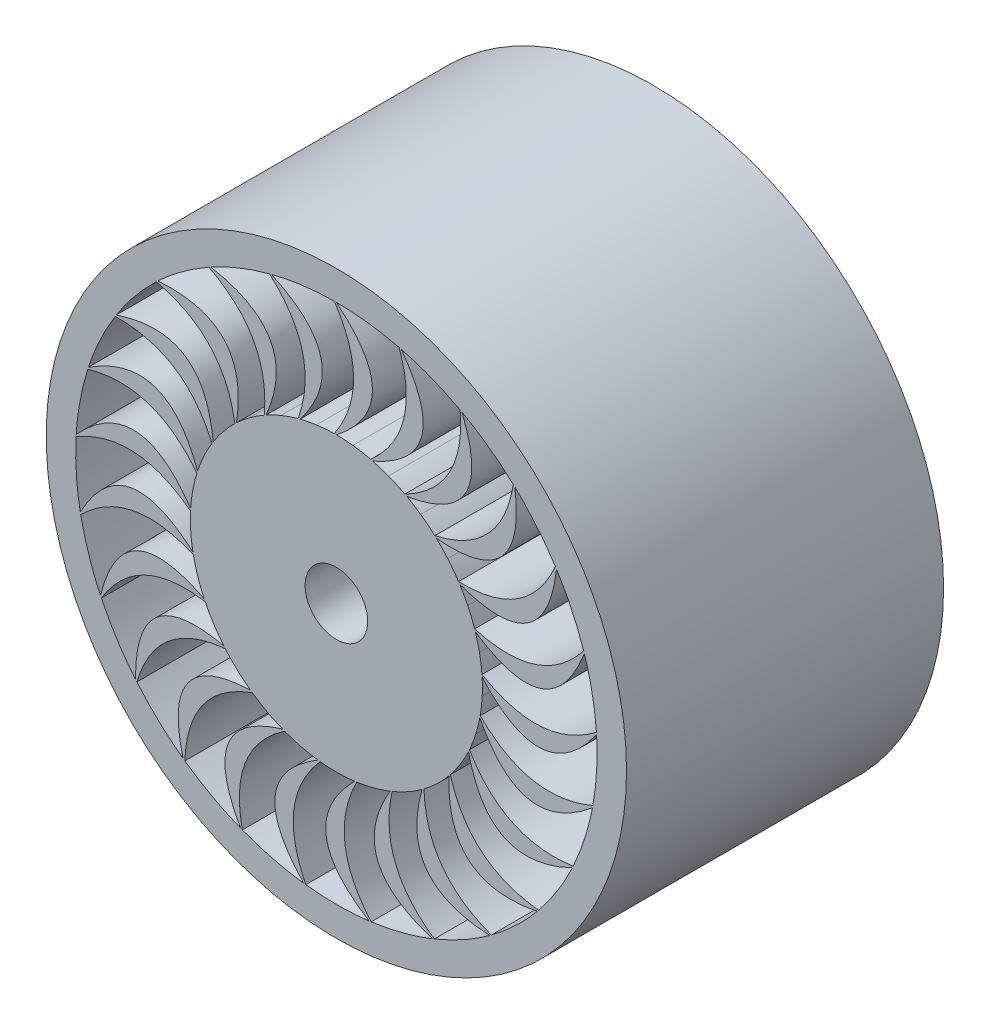
SolidWorks part; units mm, degrees
ref_plane "Front Plane" through (0, 0, 0) normal (0, 0, 1) x (1, 0, 0)
ref_plane "Top Plane" through (0, 0, 0) normal (0, 1, 0) x (1, 0, 0)
ref_plane "Right Plane" through (0, 0, 0) normal (1, 0, 0) x (0, 0, -1)
sketch "Sketch1" plane through (0, 0, 0) normal (0, 0, 1) x (1, 0, 0)
  circle A0 centre (0, 0) radius 50
  circle A1 centre (0, 0) radius 70
extrude "Boss-Extrude1" add sketch "Sketch1" along normal blind 30
sketch "Sketch2" plane through (0, 0, 30) normal (0, 0, 1) x (1, 0, 0)
  circle A0 centre (0, 0) radius 70
  circle A1 centre (0, 0) radius 34
extrude "Boss-Extrude2" add sketch "Sketch2" along normal blind 92
sketch "Sketch3" plane through (0, 0, 122) normal (0, 0, 1) x (1, 0, 0)
  circle A0 centre (0, 0) radius 15
  circle A1 centre (0, 0) radius 70
extrude "Boss-Extrude3" add sketch "Sketch3" along normal blind 30
sketch "Sketch5" plane through (0, 0, 152) normal (0, 0, 1) x (1, 0, 0)
  circle A0 centre (0, 0) radius 63.2151
  circle A1 centre (0, 0) radius 139.1054
  spline S0 degree 2 poles (0, 125) (34.5207, 97.0004) (0, 70) knots 0 0 0 1 1 1
  spline S1 degree 2 poles (-1, 124.996) (17.4362, 97.3198) (-1, 70) knots 0 0 0 1 1 1
  spline S2 degree 2 poles (30.1167, 121.3177) (41.0908, 89.9262) (16.4397, 68.0495) knots 0 0 0 1 1 1
  spline S3 degree 2 poles (31.0862, 121.0729) (57.5592, 85.368) (17.4083, 67.8008) knots 0 0 0 1 1 1
  spline S4 degree 2 poles (59.341, 110.0166) (62.1636, 76.8821) (32.8465, 61.8232) knots 0 0 0 1 1 1
  spline S5 degree 2 poles (60.2192, 109.5383) (76.981, 68.3717) (33.7228, 61.3415) knots 0 0 0 1 1 1
  spline S6 degree 2 poles (84.8367, 91.8027) (79.3304, 59.0072) (47.1893, 51.7124) knots 0 0 0 1 1 1
  spline S7 degree 2 poles (85.5684, 91.1211) (91.5659, 47.0793) (47.9183, 51.0278) knots 0 0 0 1 1 1
  spline S8 degree 2 poles (105.0018, 67.8205) (91.5126, 37.4247) (58.5671, 38.3522) knots 0 0 0 1 1 1
  spline S9 degree 2 poles (105.541, 66.9783) (100.3973, 22.8287) (59.103, 37.5079) knots 0 0 0 1 1 1
  spline S10 degree 2 poles (118.5692, 39.5769) (97.9447, 13.4907) (66.2649, 22.5822) knots 0 0 0 1 1 1
  spline S11 degree 2 poles (118.8821, 38.6271) (102.9204, -2.8563) (66.574, 21.6312) knots 0 0 0 1 1 1
  spline S12 degree 2 poles (124.6866, 8.8466) (98.2226, -11.291) (69.7991, 5.3934) knots 0 0 0 1 1 1
  spline S13 degree 2 poles (124.7533, 7.8488) (98.9766, -28.3618) (69.8619, 4.3953) knots 0 0 0 1 1 1
  spline S14 degree 2 poles (122.9694, -22.4396) (92.3288, -35.3632) (68.9475, -12.1344) knots 0 0 0 1 1 1
  spline S15 degree 2 poles (122.7859, -23.4227) (88.8138, -52.0853) (68.7601, -13.1167) knots 0 0 0 1 1 1
  spline S16 degree 2 poles (113.5255, -52.3159) (80.6337, -57.2135) (63.7637, -28.8997) knots 0 0 0 1 1 1
  spline S17 degree 2 poles (113.1034, -53.2224) (73.0704, -72.536) (63.3379, -29.8046) knots 0 0 0 1 1 1
  spline S18 degree 2 poles (96.9485, -78.9049) (63.872, -75.4688) (54.5734, -43.8492) knots 0 0 0 1 1 1
  spline S19 degree 2 poles (96.3142, -79.678) (52.7358, -88.429) (53.9359, -44.6197) knots 0 0 0 1 1 1
  spline S20 degree 2 poles (74.2798, -100.5361) (43.097, -88.9821) (41.954, -56.0434) knots 0 0 0 1 1 1
  spline S21 degree 2 poles (73.4732, -101.1271) (29.0876, -98.7657) (41.145, -56.6312) knots 0 0 0 1 1 1
  spline S22 degree 2 poles (46.9439, -115.8502) (19.6141, -96.9044) (26.6985, -64.7162) knots 0 0 0 1 1 1
  spline S23 degree 2 poles (46.0156, -116.2221) (3.6117, -102.8966) (25.7687, -65.0844) knots 0 0 0 1 1 1
  spline S24 degree 2 poles (16.6583, -123.885) (-5.1013, -98.7378) (9.7654, -69.3227) knots 0 0 0 1 1 1
  spline S25 degree 2 poles (15.6667, -124.0143) (-22.0911, -100.5621) (8.7733, -69.448) knots 0 0 0 1 1 1
  spline S26 degree 2 poles (-14.674, -124.1357) (-29.4961, -94.3671) (-7.7812, -69.5734) knots 0 0 0 1 1 1
  spline S27 degree 2 poles (-15.6667, -124.0143) (-46.4058, -91.909) (-8.7733, -69.448) knots 0 0 0 1 1 1
  spline S28 degree 2 poles (-45.0843, -116.5865) (-52.0376, -84.067) (-24.8389, -65.4525) knots 0 0 0 1 1 1
  spline S29 degree 2 poles (-46.0156, -116.2221) (-67.8047, -77.4808) (-25.7687, -65.0844) knots 0 0 0 1 1 1
  spline S30 degree 2 poles (-72.6618, -101.7117) (-71.3093, -68.4847) (-40.336, -57.219) knots 0 0 0 1 1 1
  spline S31 degree 2 poles (-73.4732, -101.1271) (-84.9432, -58.1843) (-41.145, -56.6312) knots 0 0 0 1 1 1
  spline S32 degree 2 poles (-95.6737, -80.446) (-86.1005, -48.5992) (-53.2985, -45.3902) knots 0 0 0 1 1 1
  spline S33 degree 2 poles (-96.3142, -79.678) (-96.7444, -35.2318) (-53.9359, -44.6197) knots 0 0 0 1 1 1
  spline S34 degree 2 poles (-112.674, -54.1255) (-95.4816, -25.6601) (-62.9121, -30.7094) knots 0 0 0 1 1 1
  spline S35 degree 2 poles (-113.1034, -53.2224) (-102.4668, -10.0655) (-63.3379, -29.8046) knots 0 0 0 1 1 1
  spline S36 degree 2 poles (-122.5946, -24.4042) (-98.8633, -1.1086) (-68.5727, -14.099) knots 0 0 0 1 1 1
  spline S37 degree 2 poles (-122.7859, -23.4227) (-101.7508, 15.7331) (-68.7601, -13.1167) knots 0 0 0 1 1 1
  spline S38 degree 2 poles (-124.8121, 6.8505) (-96.033, 23.5125) (-69.9247, 3.3973) knots 0 0 0 1 1 1
  spline S39 degree 2 poles (-124.7533, 7.8488) (-94.6415, 40.5433) (-69.8619, 4.3953) knots 0 0 0 1 1 1
  spline S40 degree 2 poles (-119.1873, 37.6748) (-87.1686, 46.6563) (-66.883, 20.6801) knots 0 0 0 1 1 1
  spline S41 degree 2 poles (-118.8821, 38.6271) (-81.5854, 62.8059) (-66.574, 21.6312) knots 0 0 0 1 1 1
  spline S42 degree 2 poles (-106.0734, 66.1319) (-72.8271, 66.8684) (-59.6388, 36.6635) knots 0 0 0 1 1 1
  spline S43 degree 2 poles (-105.541, 66.9783) (-63.4031, 81.1222) (-59.103, 37.5079) knots 0 0 0 1 1 1
  spline S44 degree 2 poles (-86.2946, 90.4336) (-53.9096, 82.879) (-48.6473, 50.3433) knots 0 0 0 1 1 1
  spline S45 degree 2 poles (-85.5684, 91.1211) (-41.2369, 94.3413) (-47.9183, 51.0278) knots 0 0 0 1 1 1
  spline S46 degree 2 poles (-61.0936, 109.0531) (-31.6048, 93.682) (-34.5991, 60.8597) knots 0 0 0 1 1 1
  spline S47 degree 2 poles (-60.2192, 109.5383) (-16.4796, 101.6326) (-33.7228, 61.3415) knots 0 0 0 1 1 1
  spline S48 degree 2 poles (-32.0538, 120.8203) (-7.3141, 98.5986) (-18.3769, 67.5521) knots 0 0 0 1 1 1
  spline S49 degree 2 poles (-31.0862, 121.0729) (9.3131, 102.5379) (-17.4083, 67.8008) knots 0 0 0 1 1 1
  spline S50 degree 2 poles (0, 125) (15.3959, 124.9712) (30.1167, 121.3177) knots 0 0 0 0.038773 0.038773 0.038773
  spline S51 degree 2 poles (-31.0862, 121.0729) (-16.3951, 124.8441) (-1, 124.996) knots 0.961227 0.961227 0.961227 1 1 1
  spline S52 degree 3 poles (-60.2192, 109.5383) (-51.3556, 114.4105) (-41.8313, 118.2258) (-32.0538, 120.8203) knots 0.921176 0.921176 0.921176 0.921176 0.959949 0.959949 0.959949 0.959949
  spline S53 degree 3 poles (-85.5684, 91.1211) (-78.1949, 98.0445) (-69.9174, 104.1091) (-61.0936, 109.0531) knots 0.881125 0.881125 0.881125 0.881125 0.919898 0.919898 0.919898 0.919898
  spline S54 degree 3 poles (-105.541, 66.9783) (-100.1209, 75.518) (-93.6117, 83.4506) (-86.2946, 90.4336) knots 0.841073 0.841073 0.841073 0.841073 0.879847 0.879847 0.879847 0.879847
  spline S55 degree 3 poles (-118.8821, 38.6271) (-115.756, 48.2464) (-111.4241, 57.5486) (-106.0734, 66.1319) knots 0.801022 0.801022 0.801022 0.801022 0.839796 0.839796 0.839796 0.839796
  spline S56 degree 3 poles (-122.7859, -23.4227) (-124.6806, -13.4873) (-125.3659, -3.2487) (-124.8121, 6.8505) knots 0.72092 0.72092 0.72092 0.72092 0.759693 0.759693 0.759693 0.759693
  spline S57 degree 3 poles (-124.7533, 7.8488) (-124.1177, 17.9433) (-122.2352, 28.0305) (-119.1873, 37.6748) knots 0.760971 0.760971 0.760971 0.760971 0.799744 0.799744 0.799744 0.799744
  spline S58 degree 3 poles (-96.3142, -79.678) (-102.7609, -71.8843) (-108.2939, -63.2424) (-112.674, -54.1255) knots 0.640818 0.640818 0.640818 0.640818 0.679591 0.679591 0.679591 0.679591
  spline S59 degree 3 poles (-113.1034, -53.2224) (-117.4094, -44.0703) (-120.6193, -34.3239) (-122.5946, -24.4042) knots 0.680869 0.680869 0.680869 0.680869 0.719642 0.719642 0.719642 0.719642
  spline S60 degree 3 poles (-73.4732, -101.1271) (-81.6556, -95.1815) (-89.1639, -88.1871) (-95.6737, -80.446) knots 0.600767 0.600767 0.600767 0.600767 0.63954 0.63954 0.63954 0.63954
  spline S61 degree 3 poles (-46.0156, -116.2221) (-55.4195, -112.4981) (-64.4314, -107.5907) (-72.6618, -101.7117) knots 0.560716 0.560716 0.560716 0.560716 0.599489 0.599489 0.599489 0.599489
  spline S62 degree 3 poles (-15.6667, -124.0143) (-25.7013, -122.7461) (-35.6504, -120.234) (-45.0843, -116.5865) knots 0.520665 0.520665 0.520665 0.520665 0.559438 0.559438 0.559438 0.559438
  spline S63 degree 3 poles (15.6667, -124.0143) (5.6319, -125.2814) (-4.6295, -125.3225) (-14.674, -124.1357) knots 0.480613 0.480613 0.480613 0.480613 0.519387 0.519387 0.519387 0.519387
  spline S64 degree 3 poles (46.0156, -116.2221) (36.6112, -119.9449) (26.6824, -122.5366) (16.6583, -123.885) knots 0.440562 0.440562 0.440562 0.440562 0.479335 0.479335 0.479335 0.479335
  spline S65 degree 3 poles (73.4732, -101.1271) (65.29, -107.0718) (56.3177, -112.0512) (46.9439, -115.8502) knots 0.400511 0.400511 0.400511 0.400511 0.439284 0.439284 0.439284 0.439284
  spline S66 degree 3 poles (96.3142, -79.678) (89.8665, -87.471) (82.4144, -94.5252) (74.2798, -100.5361) knots 0.36046 0.36046 0.36046 0.36046 0.399233 0.399233 0.399233 0.399233
  spline S67 degree 3 poles (113.1034, -53.2224) (108.7963, -62.374) (103.3327, -71.0599) (96.9485, -78.9049) knots 0.320409 0.320409 0.320409 0.320409 0.359182 0.359182 0.359182 0.359182
  spline S68 degree 3 poles (122.7859, -23.4227) (120.8901, -33.3579) (117.7582, -43.1297) (113.5255, -52.3159) knots 0.280358 0.280358 0.280358 0.280358 0.319131 0.319131 0.319131 0.319131
  spline S69 degree 3 poles (124.7533, 7.8488) (125.3879, -2.2457) (124.7845, -12.4894) (122.9694, -22.4396) knots 0.240307 0.240307 0.240307 0.240307 0.27908 0.27908 0.27908 0.27908
  spline S70 degree 3 poles (118.8821, 38.6271) (122.0071, 29.0075) (123.9702, 18.9356) (124.6866, 8.8466) knots 0.200256 0.200256 0.200256 0.200256 0.239029 0.239029 0.239029 0.239029
  spline S71 degree 3 poles (105.541, 66.9783) (110.9601, 58.4381) (115.3663, 49.1709) (118.5692, 39.5769) knots 0.160204 0.160204 0.160204 0.160204 0.198978 0.198978 0.198978 0.198978
  spline S72 degree 3 poles (85.5684, 91.1211) (92.9411, 84.1968) (99.5136, 76.3165) (105.0018, 67.8205) knots 0.120153 0.120153 0.120153 0.120153 0.158927 0.158927 0.158927 0.158927
  spline S73 degree 3 poles (60.2192, 109.5383) (69.0823, 104.6651) (77.408, 98.6669) (84.8367, 91.8027) knots 0.080102 0.080102 0.080102 0.080102 0.118875 0.118875 0.118875 0.118875
  spline S74 degree 3 poles (31.0862, 121.0729) (40.8841, 118.5567) (50.4387, 114.8177) (59.341, 110.0166) knots 0.040051 0.040051 0.040051 0.040051 0.078824 0.078824 0.078824 0.078824
  spline S75 degree 3 poles (-59.103, 37.5079) (-56.1136, 42.1483) (-52.6408, 46.535) (-48.6473, 50.3433) knots 0 0 0 0 0.037721 0.037721 0.037721 0.037721
  spline S76 degree 3 poles (-66.574, 21.6312) (-64.8325, 26.8692) (-62.5598, 31.9818) (-59.6388, 36.6635) knots 0.96 0.96 0.96 0.96 0.997721 0.997721 0.997721 0.997721
  spline S77 degree 3 poles (-69.8619, 4.3953) (-69.4778, 9.9019) (-68.5479, 15.419) (-66.883, 20.6801) knots 0.92 0.92 0.92 0.92 0.957721 0.957721 0.957721 0.957721
  spline S78 degree 3 poles (-68.7601, -13.1167) (-69.7575, -7.6876) (-70.2289, -2.1126) (-69.9247, 3.3973) knots 0.88 0.88 0.88 0.88 0.917721 0.917721 0.917721 0.917721
  spline S79 degree 3 poles (-63.3379, -29.8046) (-65.6541, -24.7941) (-67.4972, -19.5114) (-68.5727, -14.099) knots 0.84 0.84 0.84 0.84 0.877721 0.877721 0.877721 0.877721
  spline S80 degree 3 poles (-53.9359, -44.6197) (-57.4254, -40.3426) (-60.5244, -35.6843) (-62.9121, -30.7094) knots 0.8 0.8 0.8 0.8 0.837721 0.837721 0.837721 0.837721
  spline S81 degree 3 poles (-41.145, -56.6312) (-45.5885, -53.3563) (-49.7485, -49.615) (-53.2985, -45.3902) knots 0.76 0.76 0.76 0.76 0.797721 0.797721 0.797721 0.797721
  spline S82 degree 3 poles (-25.7687, -65.0844) (-30.8871, -63.0174) (-35.8469, -60.4282) (-40.336, -57.219) knots 0.72 0.72 0.72 0.72 0.757721 0.757721 0.757721 0.757721
  spline S83 degree 3 poles (-8.7733, -69.448) (-14.2449, -68.7189) (-19.6928, -67.4445) (-24.8389, -65.4525) knots 0.68 0.68 0.68 0.68 0.717721 0.717721 0.717721 0.717721
  spline S84 degree 3 poles (8.7733, -69.448) (3.2923, -70.1026) (-2.3013, -70.223) (-7.7812, -69.5734) knots 0.64 0.64 0.64 0.64 0.677721 0.677721 0.677721 0.677721
  spline S85 degree 3 poles (25.7687, -65.0844) (20.6227, -67.0814) (15.2347, -68.5891) (9.7654, -69.3227) knots 0.6 0.6 0.6 0.6 0.637721 0.637721 0.637721 0.637721
  spline S86 degree 3 poles (41.145, -56.6312) (36.6573, -59.8453) (31.8135, -62.6456) (26.6985, -64.7162) knots 0.56 0.56 0.56 0.56 0.597721 0.597721 0.597721 0.597721
  spline S87 degree 3 poles (53.9359, -44.6197) (50.3885, -48.8488) (46.3934, -52.7657) (41.954, -56.0434) knots 0.52 0.52 0.52 0.52 0.557721 0.557721 0.557721 0.557721
  spline S88 degree 3 poles (63.3379, -29.8046) (60.9537, -34.783) (58.0581, -39.5704) (54.5734, -43.8492) knots 0.48 0.48 0.48 0.48 0.517721 0.517721 0.517721 0.517721
  spline S89 degree 3 poles (68.7601, -13.1167) (67.6889, -18.5317) (66.0749, -23.8888) (63.7637, -28.8997) knots 0.44 0.44 0.44 0.44 0.477721 0.477721 0.477721 0.477721
  spline S90 degree 3 poles (69.8619, 4.3953) (70.171, -1.1159) (69.9399, -6.7061) (68.9475, -12.1344) knots 0.4 0.4 0.4 0.4 0.437721 0.437721 0.437721 0.437721
  spline S91 degree 3 poles (66.574, 21.6312) (68.2439, 16.3699) (69.4104, 10.8979) (69.7991, 5.3934) knots 0.36 0.36 0.36 0.36 0.397721 0.397721 0.397721 0.397721
  spline S92 degree 3 poles (59.103, 37.5079) (62.0289, 32.8272) (64.5195, 27.8172) (66.2649, 22.5822) knots 0.32 0.32 0.32 0.32 0.357721 0.357721 0.357721 0.357721
  spline S93 degree 3 poles (47.9183, 51.0278) (51.9163, 47.2218) (55.5747, 42.9886) (58.5671, 38.3522) knots 0.28 0.28 0.28 0.28 0.317721 0.317721 0.317721 0.317721
  spline S94 degree 3 poles (33.7228, 61.3415) (38.5417, 58.6493) (43.1379, 55.4589) (47.1893, 51.7124) knots 0.24 0.24 0.24 0.24 0.277721 0.277721 0.277721 0.277721
  spline S95 degree 3 poles (17.4083, 67.8008) (22.7453, 66.3917) (27.9905, 64.4445) (32.8465, 61.8232) knots 0.2 0.2 0.2 0.2 0.237721 0.237721 0.237721 0.237721
  spline S96 degree 3 poles (0, 70) (5.5198, 69.9624) (11.0845, 69.3808) (16.4397, 68.0495) knots 0.16 0.16 0.16 0.16 0.197721 0.197721 0.197721 0.197721
  spline S97 degree 3 poles (-17.4083, 67.8008) (-12.0525, 69.1371) (-6.5181, 69.9577) (-1, 70) knots 0.12 0.12 0.12 0.12 0.157721 0.157721 0.157721 0.157721
  spline S98 degree 3 poles (-33.7228, 61.3415) (-28.8676, 63.9677) (-23.7111, 66.1389) (-18.3769, 67.5521) knots 0.08 0.08 0.08 0.08 0.117721 0.117721 0.117721 0.117721
  spline S99 degree 3 poles (-47.9183, 51.0278) (-43.8688, 54.779) (-39.4142, 58.1643) (-34.5991, 60.8597) knots 0.04 0.04 0.04 0.04 0.077721 0.077721 0.077721 0.077721
  point P156 (0, 0)
extrude "Boss-Extrude4" add sketch "Sketch5" against normal blind 152
